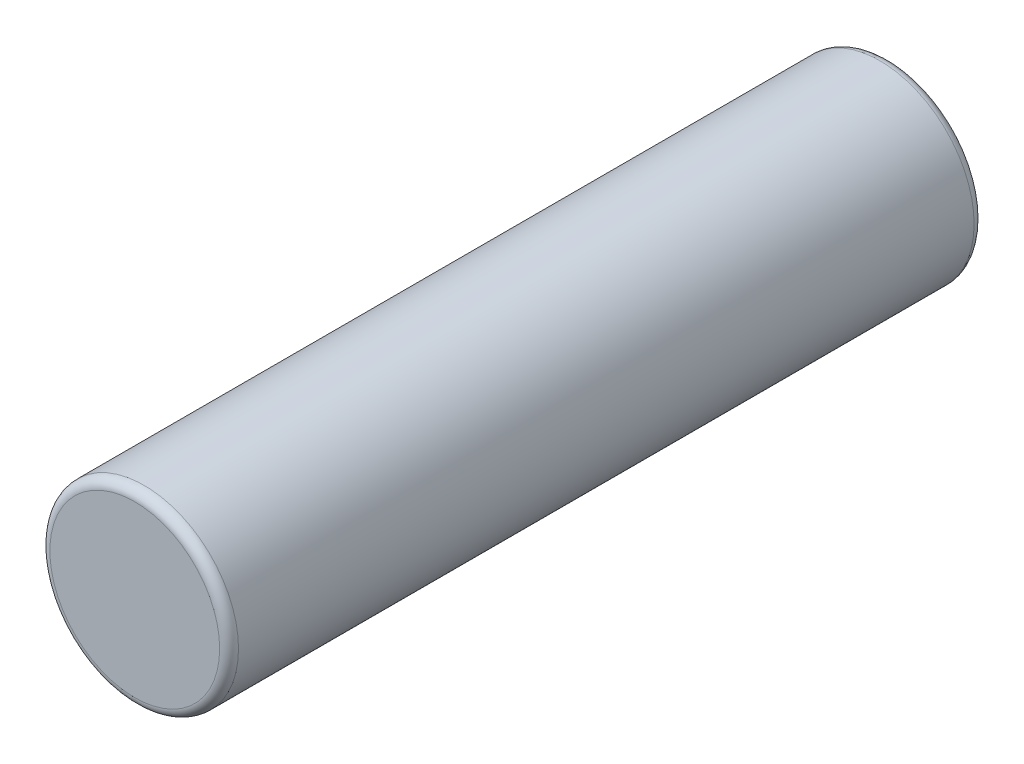
SolidWorks part; units mm, degrees
ref_plane "Front Plane" through (0, 0, 0) normal (0, 0, 1) x (1, 0, 0)
ref_plane "Top Plane" through (0, 0, 0) normal (0, 1, 0) x (1, 0, 0)
ref_plane "Right Plane" through (0, 0, 0) normal (1, 0, 0) x (0, 0, -1)
sketch "Sketch1" plane through (0, 0, 0) normal (0, 0, 1) x (1, 0, 0)
  circle A0 centre (0, 0) radius 1.27
  dimension "D1" = 2.54
extrude "Boss-Extrude1" add sketch "Sketch1" along normal blind 10.16
fillet "Fillet1" radius 0.127 1 edges at (1.27, 0, 10.16)
fillet "Fillet2" radius 0.127 1 edges at (1.27, 0, 0)
